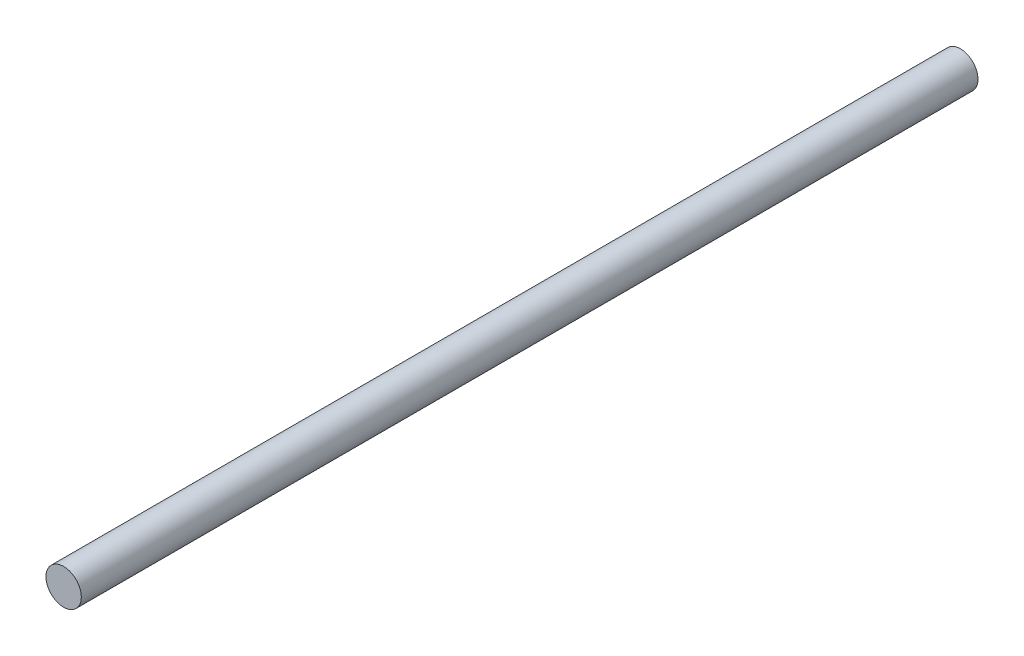
SolidWorks part; units mm, degrees
ref_plane "前视基准面" through (0, 0, 0) normal (0, 0, 1) x (1, 0, 0)
ref_plane "上视基准面" through (0, 0, 0) normal (0, 1, 0) x (1, 0, 0)
ref_plane "右视基准面" through (0, 0, 0) normal (1, 0, 0) x (0, 0, -1)
sketch "草图1" plane through (0, 0, 0) normal (0, 0, 1) x (1, 0, 0)
  circle A0 centre (0, 0) radius 4
  dimension "D1" = 8
extrude "凸台-拉伸1" add sketch "草图1" along normal mid plane 203
